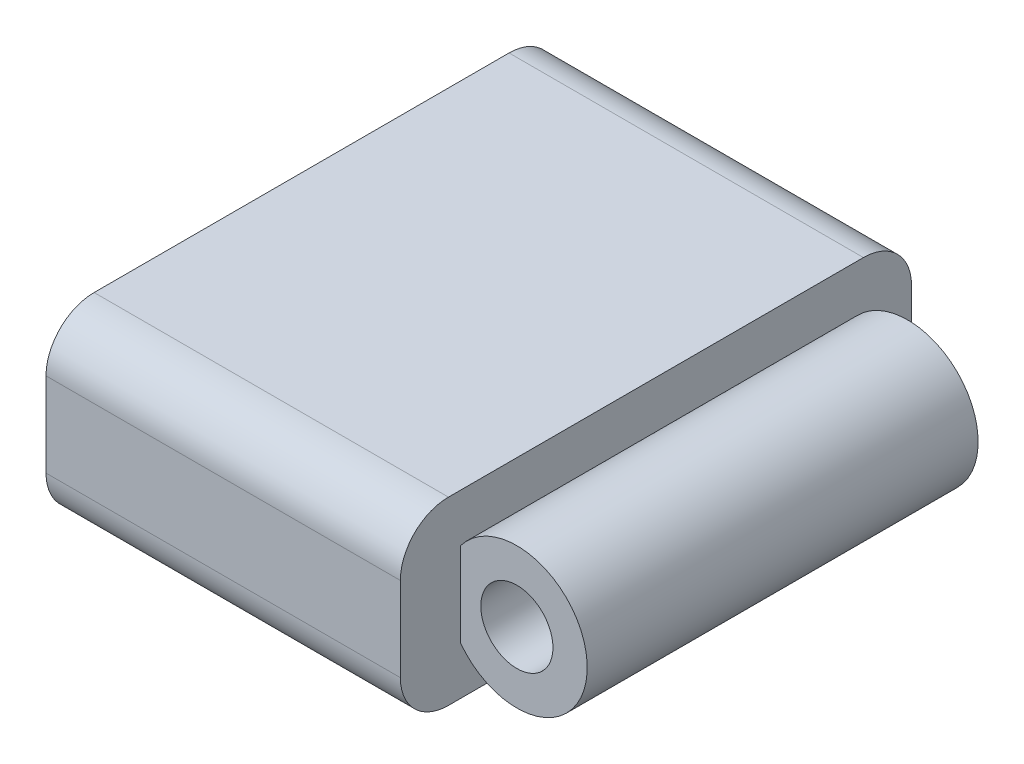
SolidWorks part; units mm, degrees
material "PTFE (general)"
ref_plane "Front Plane" through (0, 0, 0) normal (0, 0, 1) x (1, 0, 0)
ref_plane "Top Plane" through (0, 0, 0) normal (0, 1, 0) x (1, 0, 0)
ref_plane "Right Plane" through (0, 0, 0) normal (1, 0, 0) x (0, 0, -1)
sketch "Sketch1" plane through (0, 0, 0) normal (0, 1, 0) x (1, 0, 0)
  line L1 (0, 0) -> (50.8, 0)
  line L2 (0, 0) -> (0, 53.975)
  line L3 (0, 53.975) -> (50.8, 53.975)
  line L4 (50.8, 0) -> (50.8, 53.975)
  dimension "D1" = 50.8
  dimension "D2" = 53.975
extrude "Boss-Extrude1" add sketch "Sketch1" along normal blind 19.05
fillet "Fillet1" radius 5.08 4 edges at (25.4, 0, -53.975) (25.4, 0, 0) (25.4, 19.05, -53.975) (25.4, 19.05, 0)
sketch "Sketch2" plane through (0, 0, 0) normal (0, 0, 1) x (1, 0, 0)
  line L0 (50.8, 9.525) -> (0, 9.525) construction
  line L1 (50.8, 13.97) -> (50.8, 5.08) construction
  line L2 (0, 13.97) -> (0, 5.08) construction
  line L3 (37.4174, 19.05) -> (37.4174, 13.97)
  line L4 (0, 19.05) -> (50.8, 19.05) construction
  line L5 (50.8, 13.97) -> (0, 13.97) construction
  line L6 (37.4174, 5.08) -> (37.4174, 0)
  line L7 (50.8, 0) -> (0, 0) construction
  line L8 (37.4174, 19.05) -> (50.8, 19.05)
  line L9 (50.8, 19.05) -> (50.8, 9.525)
  line L10 (37.4174, 0) -> (50.8, 0)
  line L11 (50.8, 0) -> (50.8, 9.525)
  circle A0 centre (43.3705, 9.525) radius 7.4295
  line M3 (0, 5.08) -> (50.8, 5.08)
  line M4 (50.8, 5.08) -> (50.8, 13.97)
  line M5 (50.8, 13.97) -> (0, 13.97)
  dimension "D1" = 14.859
extrude "Cut-Extrude1" cut sketch "Sketch2" against normal through all contours A0 L9 L8 L3 M5 | A0 M4 M5 | A0 M3 M4 | A0 L6 L10 L11 M3
sketch "Sketch3" plane through (0, 19.05, 0) normal (0, 1, 0) x (1, 0, 0)
  line L1 (37.4174, 0) -> (52.1675, 0)
  line L2 (37.4174, 0) -> (37.4174, 6.35)
  line L3 (37.4174, 6.35) -> (52.1675, 6.35)
  line L4 (52.1675, 0) -> (52.1675, 6.35)
  line L5 (37.4174, 53.975) -> (54.6314, 53.975)
  line L6 (37.4174, 53.975) -> (37.4174, 47.625)
  line L7 (37.4174, 47.625) -> (54.6314, 47.625)
  line L8 (54.6314, 53.975) -> (54.6314, 47.625)
  dimension "D1" = 6.35
  dimension "D2" = 6.35
extrude "Cut-Extrude2" cut sketch "Sketch3" against normal blind 19.05
sketch "Sketch4" plane through (0, 0, -6.35) normal (0, 0, 1) x (1, 0, 0)
  circle A0 centre (43.3705, 9.525) radius 3.81
  dimension "D1" = 7.62
extrude "Cut-Extrude3" cut sketch "Sketch4" against normal through all
sketch "Sketch5" plane through (0, 0, 0) normal (-1, 0, 0) x (0, 0, 1)
  line L0 (-26.9875, 19.05) -> (-26.9875, 0) construction
  line L1 (-48.895, 19.05) -> (-5.08, 19.05) construction
  line L2 (-48.895, 0) -> (-5.08, 0) construction
  line L3 (-53.975, 9.525) -> (0, 9.525) construction
  line L4 (-53.975, 13.97) -> (-53.975, 5.08) construction
  line L5 (0, 13.97) -> (0, 5.08) construction
  line L7 (-6.6675, 1.905) -> (-47.3075, 1.905)
  line L8 (-6.6675, 1.905) -> (-6.6675, 17.145)
  line L9 (-6.6675, 17.145) -> (-47.3075, 17.145)
  line L10 (-47.3075, 1.905) -> (-47.3075, 17.145)
  line L11 (-6.6675, 1.905) -> (-47.3075, 17.145) construction
  line L12 (-6.6675, 17.145) -> (-47.3075, 1.905) construction
  point P12 (-26.9875, 9.525)
  dimension "D1" = 40.64
  dimension "D2" = 15.24
extrude "Cut-Extrude4" cut sketch "Sketch5" against normal blind 17.78
fillet "Fillet2" radius 2.54 4 edges at (8.89, 17.145, -6.6675) (8.89, 1.905, -6.6675) (8.89, 1.905, -47.3075) (8.89, 17.145, -47.3075)
